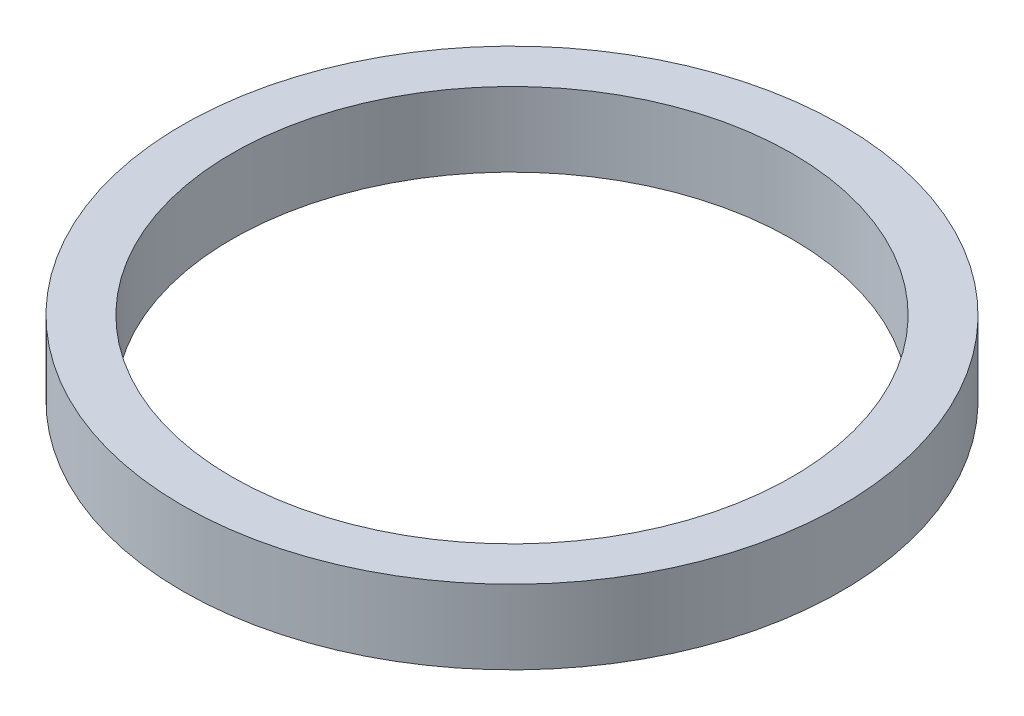
SolidWorks part; units mm, degrees
material "6061-T6 (SS)"
ref_plane "Front Plane" through (0, 0, 0) normal (0, 0, 1) x (1, 0, 0)
ref_plane "Top Plane" through (0, 0, 0) normal (0, 1, 0) x (1, 0, 0)
ref_plane "Right Plane" through (0, 0, 0) normal (1, 0, 0) x (0, 0, -1)
sketch "Sketch1" plane through (0, 0, 0) normal (0, 1, 0) x (1, 0, 0)
  circle A0 centre (0, 0) radius 25.4
  circle A1 centre (0, 0) radius 21.59
  dimension "D1" = 50.8
  dimension "D2" = 3.81
extrude "Boss-Extrude1" add sketch "Sketch1" along normal blind 5.715
